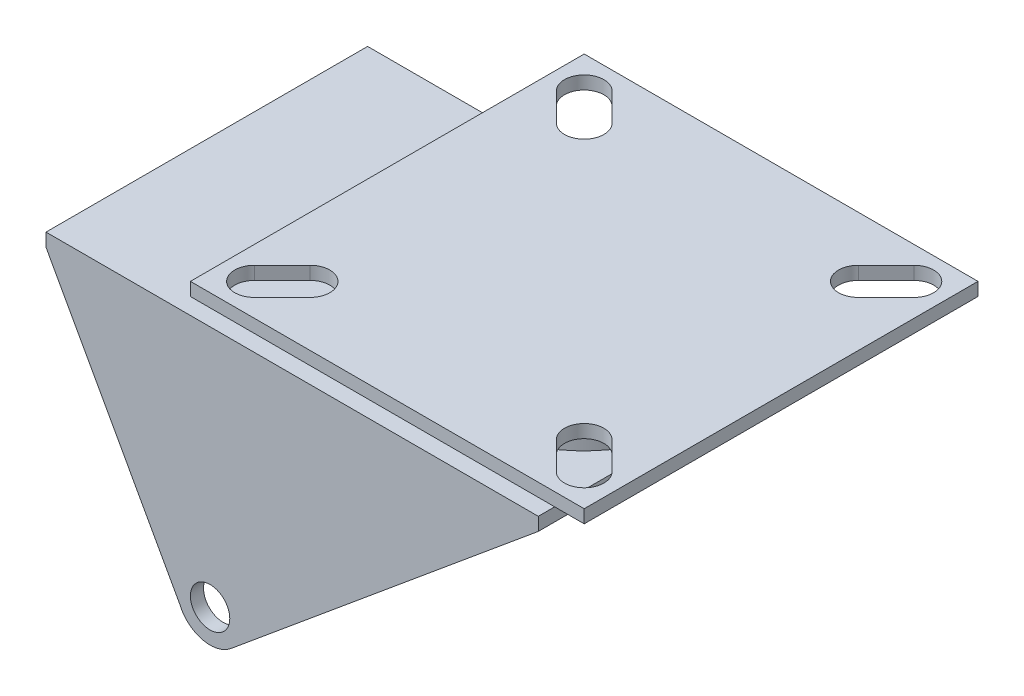
SolidWorks part; units mm, degrees
ref_plane "Front Plane" through (0, 0, 0) normal (0, 0, 1) x (1, 0, 0)
ref_plane "Top Plane" through (0, 0, 0) normal (0, 1, 0) x (1, 0, 0)
ref_plane "Right Plane" through (0, 0, 0) normal (1, 0, 0) x (0, 0, -1)
sketch "Sketch1" plane through (0, 0, 0) normal (0, 0, 1) x (1, 0, 0)
  line L0 (-25, 35) -> (-4.6192, -1.9138)
  line L1 (-25, 35) -> (50, 35)
  line L2 (50, 35) -> (3.1932, -3.8475)
  circle A0 centre (0, 0) radius 5
  circle A1 centre (0, 0) radius 3
  dimension "D4" = 10
  dimension "D5" = 6
  dimension "D1" = 35
  dimension "D2" = 75
  dimension "D3" = 50
extrude "Boss-Extrude1" add sketch "Sketch1" along normal blind 2 from offset 2 contours A0 L2 L1 L0 | A0 A1
ref_plane "Plane4" through (0, 0, -20.5) normal (0, 0, -1) x (-1, 0, 0)
sketch "Sketch2" plane through (0, 0, -41) normal (0, 0, -1) x (-1, 0, 0)
  line L3 (4.6192, -1.9138) -> (25, 35)
  line L4 (25, 35) -> (-50, 35)
  line L5 (-50, 35) -> (-3.1932, -3.8475)
  line L6 (4.6192, -1.9138) -> (25, 35)
  line L7 (25, 35) -> (-50, 35)
  line L8 (-50, 35) -> (-3.1932, -3.8475)
  circle A1 centre (0, 0) radius 22
  circle A2 centre (0, 0) radius 22
  arc A3 (-3.1932, -3.8475) -> (4.6192, -1.9138) centre (0, 0) ccw
  arc A4 (-3.1932, -3.8475) -> (4.6192, -1.9138) centre (0, 0) ccw
  circle M6 centre (0, 0) radius 22
  circle M7 centre (0, 0) radius 3
  dimension "D1" = 0
  dimension "D2" = 0
extrude "Boss-Extrude2" add sketch "Sketch2" along normal blind 2 from offset 2 separate body contours L7 L8 L6 M6 | L8 A4 L6 M6 M7
sketch "Sketch3" plane through (0, 35, 0) normal (0, 1, 0) x (1, 0, 0)
  line L1 (50, -4) -> (-25, -4)
  line L2 (50, -4) -> (50, 45)
  line L3 (50, 45) -> (-25, 45)
  line L4 (-25, -4) -> (-25, 45)
extrude "Boss-Extrude3" add sketch "Sketch3" along normal blind 2
sketch "Sketch4" plane through (0, 37, 0) normal (0, 1, 0) x (1, 0, 0)
  line L0 (-25, 20.5) -> (50, 20.5) construction
  line L1 (-25, 45) -> (-25, -4) construction
  line L2 (50, -4) -> (50, 45) construction
  circle A0 centre (32.5, 20.5) radius 17.5
  dimension "D1" = 35
extrude "Boss-Extrude4" add sketch "Sketch4" along normal blind 8
sketch "Sketch5" plane through (0, 45, 0) normal (0, 1, 0) x (1, 0, 0)
  line L0 (7.3787, 45.6213) -> (11.6213, 41.3787) construction
  line L1 (2.5, 50.5) -> (62.5, 50.5)
  line L2 (2.5, 50.5) -> (2.5, -9.5)
  line L3 (2.5, -9.5) -> (62.5, -9.5)
  line L4 (62.5, 50.5) -> (62.5, -9.5)
  line L5 (2.5, 50.5) -> (62.5, -9.5) construction
  line L6 (2.5, -9.5) -> (62.5, 50.5) construction
  line L7 (9.5, 47.7426) -> (13.7426, 43.5)
  line L8 (5.2574, 43.5) -> (9.5, 39.2574)
  line L9 (57.6213, 45.6213) -> (53.3787, 41.3787) construction
  line L10 (59.7426, 43.5) -> (55.5, 39.2574)
  line L11 (55.5, 47.7426) -> (51.2574, 43.5)
  line L12 (57.6213, -4.6213) -> (53.3787, -0.3787) construction
  line L13 (55.5, -6.7426) -> (51.2574, -2.5)
  line L14 (59.7426, -2.5) -> (55.5, 1.7426)
  line L15 (7.3787, -4.6213) -> (11.6213, -0.3787) construction
  line L16 (5.2574, -2.5) -> (9.5, 1.7426)
  line L17 (9.5, -6.7426) -> (13.7426, -2.5)
  arc A0 (9.5, 47.7426) -> (5.2574, 43.5) centre (7.3787, 45.6213) ccw
  arc A1 (9.5, 39.2574) -> (13.7426, 43.5) centre (11.6213, 41.3787) ccw
  arc A2 (59.7426, 43.5) -> (55.5, 47.7426) centre (57.6213, 45.6213) ccw
  arc A3 (51.2574, 43.5) -> (55.5, 39.2574) centre (53.3787, 41.3787) ccw
  arc A4 (55.5, -6.7426) -> (59.7426, -2.5) centre (57.6213, -4.6213) ccw
  arc A5 (55.5, 1.7426) -> (51.2574, -2.5) centre (53.3787, -0.3787) ccw
  arc A6 (5.2574, -2.5) -> (9.5, -6.7426) centre (7.3787, -4.6213) ccw
  arc A7 (13.7426, -2.5) -> (9.5, 1.7426) centre (11.6213, -0.3787) ccw
  point P0 (32.5, 20.5)
  point P8 (9.5, 43.5)
  point P18 (55.5, 43.5)
  point P25 (55.5, -2.5)
  point P32 (9.5, -2.5)
  point P37 (32.5, 20.5)
  dimension "D4" = 7
  dimension "D1" = 60
  dimension "D2" = 6
  dimension "D3" = 6
  dimension "D5" = 4
extrude "Boss-Extrude5" add sketch "Sketch5" along normal blind 2
